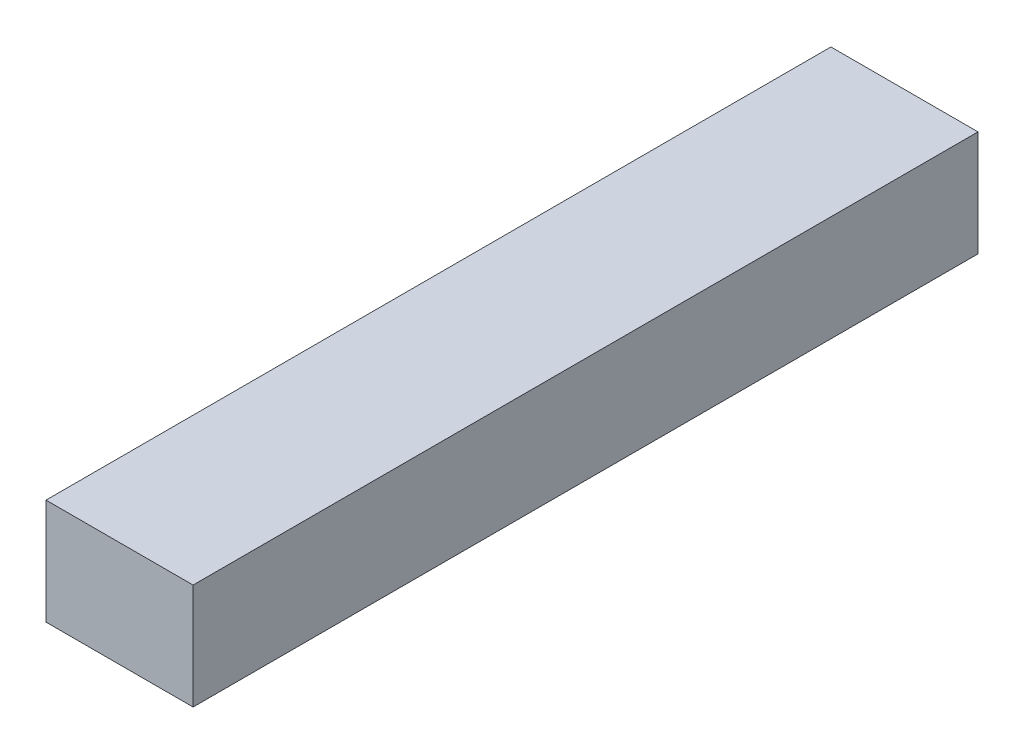
SolidWorks part; units mm, degrees
ref_plane "Front Plane" through (0, 0, 0) normal (0, 0, 1) x (1, 0, 0)
ref_plane "Top Plane" through (0, 0, 0) normal (0, 1, 0) x (1, 0, 0)
ref_plane "Right Plane" through (0, 0, 0) normal (1, 0, 0) x (0, 0, -1)
sketch "Sketch1" plane through (0, 0, 0) normal (0, 0, 1) x (1, 0, 0)
  line L0 (0, 9.15) -> (0, -10.83) construction
  line L1 (-9.75, 0) -> (21.51, 0) construction
  line L3 (2.38, -1.71) -> (-2.38, -1.71)
  line L4 (2.38, -1.71) -> (2.38, 1.71)
  line L5 (2.38, 1.71) -> (-2.38, 1.71)
  line L6 (-2.38, -1.71) -> (-2.38, 1.71)
  line L7 (2.38, -1.71) -> (-2.38, 1.71) construction
  line L8 (2.38, 1.71) -> (-2.38, -1.71) construction
  point P5 (0, 0)
  dimension "D1" = 1.71
  dimension "D2" = 4.76
extrude "Boss-Extrude1" add sketch "Sketch1" along normal blind 25.4
